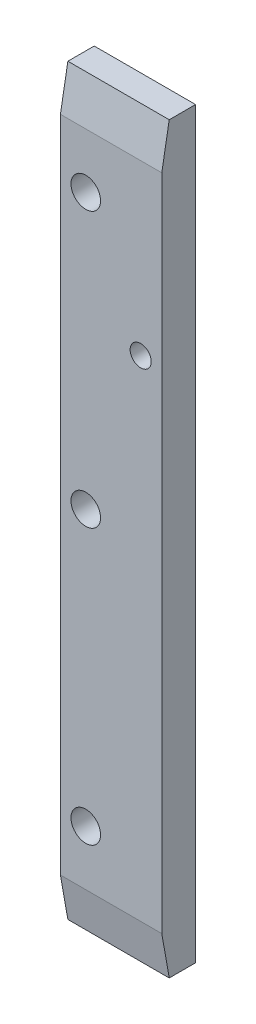
SolidWorks part; units mm, degrees
ref_plane "前视基准面" through (0, 0, 0) normal (0, 0, 1) x (1, 0, 0)
ref_plane "上视基准面" through (0, 0, 0) normal (0, 1, 0) x (1, 0, 0)
ref_plane "右视基准面" through (0, 0, 0) normal (1, 0, 0) x (0, 0, -1)
sketch "草图1" plane through (0, 0, 0) normal (0, 0, 1) x (1, 0, 0)
  line L1 (-12, 0) -> (0, 0)
  line L2 (0, 0) -> (0, -5)
  line L3 (-12, -5) -> (-12, 0)
  line L5 (0, -83) -> (0, -5)
  line L6 (-12, -5) -> (-12, -83)
  line L7 (0, -88) -> (-12, -88)
  line L8 (0, -83) -> (0, -88)
  line L9 (-12, -88) -> (-12, -83)
  line L10 (-10.925, -11.5) -> (-7.075, -11.5) construction
  line L11 (-9, -13.425) -> (-9, -9.575) construction
  line L14 (-10.925, -44) -> (-7.075, -44) construction
  line L15 (-9, -45.925) -> (-9, -42.075) construction
  line L16 (-10.925, -76.5) -> (-7.075, -76.5) construction
  line L17 (-9, -78.425) -> (-9, -74.575) construction
  circle A0 centre (-9, -76.5) radius 1.75
  circle A1 centre (-9, -44) radius 1.75
  circle A2 centre (-9, -11.5) radius 1.75
extrude "凸台-拉伸1" add sketch "草图1" along normal blind 4
hole_wizard "M3 螺纹孔1" positions "草图3" profile "草图4" tap size "M3" standard "ISO"
sketch "草图3" plane through (0, 0, 4) normal (0, 0, 1) x (1, 0, 0)
  line L0 (0, 0) -> (-12, 0) construction
  line L1 (-12, 0) -> (-12, -88) construction
  point P0 (-2.5, -25)
  dimension "D1" = 25
  dimension "D2" = 9.5
sketch "草图4" plane through (-2.5, -25, 4) normal (1, 0, 0) x (0, -1, 0)
  line L0 (0, 0) -> (0, 10.2511)
  line L1 (0, 10.2511) -> (1.25, 9.5)
  line L2 (1.25, 9.5) -> (1.25, 0)
  line L5 (1.25, 0) -> (0, 0)
  line L10 (0, 10.2511) -> (-1.25, 9.5) construction
  line L11 (0, -6.35) -> (0, 107.95) construction
  dimension "螺纹孔钻头直径" = 2.5
  dimension "螺纹孔钻头深度" = 9.5
  dimension "导头角度" = 118
cosmetic thread "孔螺蚊线1" parameters "D1"=4, "D2"=3
chamfer "倒角1" distance 5 angle 10 1 edges at (-6, -88, 4)
chamfer "倒角2" distance 5 angle 10 1 edges at (-6, 0, 4)
